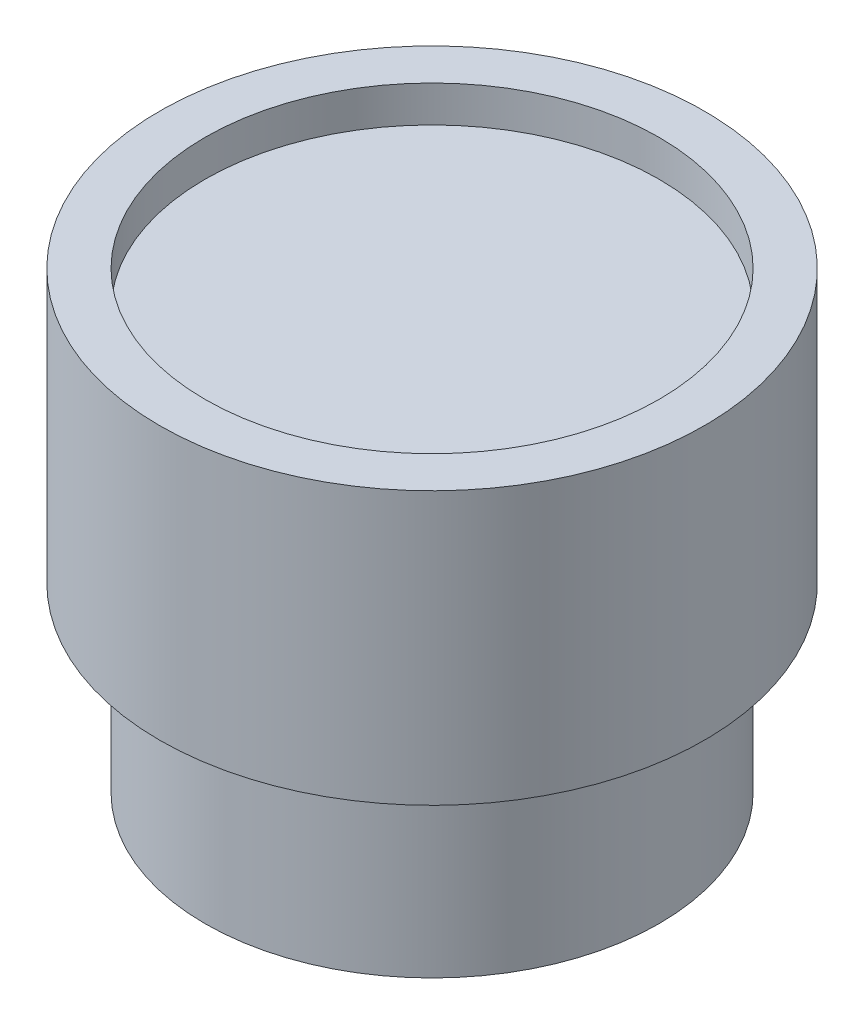
SolidWorks part; units mm, degrees
ref_plane "Front Plane" through (0, 0, 0) normal (0, 0, 1) x (1, 0, 0)
ref_plane "Top Plane" through (0, 0, 0) normal (0, 1, 0) x (1, 0, 0)
ref_plane "Right Plane" through (0, 0, 0) normal (1, 0, 0) x (0, 0, -1)
sketch "Sketch1" plane through (0, 0, 0) normal (0, 1, 0) x (1, 0, 0)
  circle A0 centre (0, 0) radius 12.5
extrude "Boss-Extrude1" add sketch "Sketch1" along normal blind 10
sketch "Sketch2" plane through (0, 10, 0) normal (0, 1, 0) x (1, 0, 0)
  circle A0 centre (0, 0) radius 15
extrude "Boss-Extrude2" add sketch "Sketch2" along normal blind 15
sketch "Sketch3" plane through (0, 25, 0) normal (0, 1, 0) x (1, 0, 0)
  circle A0 centre (0, 0) radius 12.5
extrude "Cut-Extrude1" cut sketch "Sketch3" against normal blind 2
